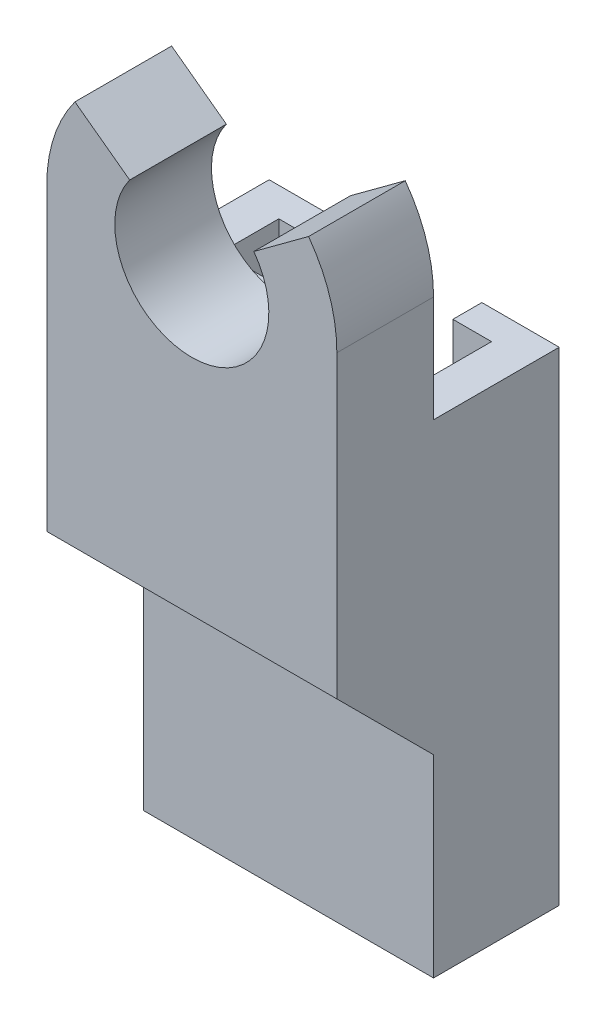
SolidWorks part; units mm, degrees
ref_plane "Front Plane" through (0, 0, 0) normal (0, 0, 1) x (1, 0, 0)
ref_plane "Top Plane" through (0, 0, 0) normal (0, 1, 0) x (1, 0, 0)
ref_plane "Right Plane" through (0, 0, 0) normal (1, 0, 0) x (0, 0, -1)
sketch "Sketch1" plane through (0, 0, 0) normal (0, 1, 0) x (1, 0, 0)
  line L0 (0, 0) -> (15, 0)
  line L1 (15, 0) -> (15, 6.5)
  line L2 (15, 6.5) -> (11, 6.5)
  line L3 (11, 6.5) -> (11, 5)
  line L4 (11, 5) -> (13, 5)
  line L5 (13, 5) -> (13, 2)
  line L6 (13, 2) -> (2, 2)
  line L7 (2, 2) -> (2, 5)
  line L8 (2, 5) -> (4, 5)
  line L9 (4, 5) -> (4, 6.5)
  line L10 (4, 6.5) -> (0, 6.5)
  line L11 (0, 6.5) -> (0, 0)
  dimension "D1" = 11
  dimension "D2" = 3
  dimension "D3" = 2
  dimension "D4" = 3
  dimension "D5" = 2
  dimension "D6" = 1.5
  dimension "D7" = 1.5
  dimension "D8" = 2
  dimension "D9" = 2
  dimension "D10" = 2
extrude "Boss-Extrude2" add sketch "Sketch1" along normal blind 25
sketch "Sketch2" plane through (0, 25, 0) normal (0, 1, 0) x (1, 0, 0)
  line L0 (7.5, 0) -> (7.5, -13.6617) construction
  line L1 (0, 0) -> (15, 0) construction
  line L3 (15, -8) -> (15, 0)
  line L4 (15, 0) -> (0, 0)
  line L5 (0, 0) -> (14.5313, -15.5) construction
  line L6 (15, 0) -> (0.8778, -15.0637) construction
  line L7 (10.2358, -10.9181) -> (12.6296, -13.4715)
  line L8 (4.7642, -10.9181) -> (2.3704, -13.4715)
  line L9 (0, 0) -> (0, -8)
  arc A0 (10.2358, -10.9181) -> (4.7642, -10.9181) centre (7.5, -8) ccw
  arc A1 (12.6296, -13.4715) -> (15, -8) centre (7.5, -8) ccw
  arc A2 (0, -8) -> (2.3704, -13.4715) centre (7.5, -8) ccw
  point P15 (10.2358, -10.9181)
sketch "Sketch3" plane through (0, 0, 0) normal (0, 0, 1) x (1, 0, 0)
  line L0 (15, 25) -> (15, 28.2916)
  line L1 (15, 25) -> (15, 15)
  line L2 (0, 25) -> (0, 28.2916)
  line L3 (7.5, 25) -> (7.5, 43.9884) construction
  line L4 (0, 25) -> (15.6207, 36.5113) construction
  line L5 (15, 25) -> (-1.5299, 37.1644) construction
  line L6 (15, 28.2916) -> (15, 30.5)
  line L7 (0, 28.2916) -> (0, 30.5)
  line L8 (13.5377, 34.9762) -> (10.7072, 32.8904)
  line L9 (4.2876, 32.8833) -> (1.4557, 34.9673)
  line L10 (15, 25) -> (15, 0) construction
  line L11 (15, 15) -> (0, 15)
  line L12 (0, 25) -> (0, 0) construction
  line L13 (0, 15) -> (0, 25)
  arc A0 (10.7072, 32.8904) -> (4.2876, 32.8833) centre (7.5, 30.5269) cw
  arc A1 (15, 30.5) -> (13.5377, 34.9762) centre (7.5, 30.5269) ccw
  arc A2 (0, 30.5) -> (1.4557, 34.9673) centre (7.5, 30.5269) cw
  point P16 (13.487, 35.0173)
  point P17 (1.4686, 34.9578)
  point P18 (10.7072, 32.8904)
  point P19 (4.2876, 32.8833)
  dimension "D1" = 10
extrude "Boss-Extrude4" add sketch "Sketch3" along normal blind 5
sketch "Sketch4" plane through (15, 0, 0) normal (1, 0, 0) x (0, 0, -1)
  line L0 (-5, 15) -> (0, 10)
  line L1 (0, 15) -> (0, 0) construction
  line L2 (0, 10) -> (0, 15)
  line L3 (0, 15) -> (-5, 15)
extrude "Boss-Extrude5" add sketch "Sketch4" against normal up to surface (15 mm away) up to face at (0, 18.9063, -0.4687)
